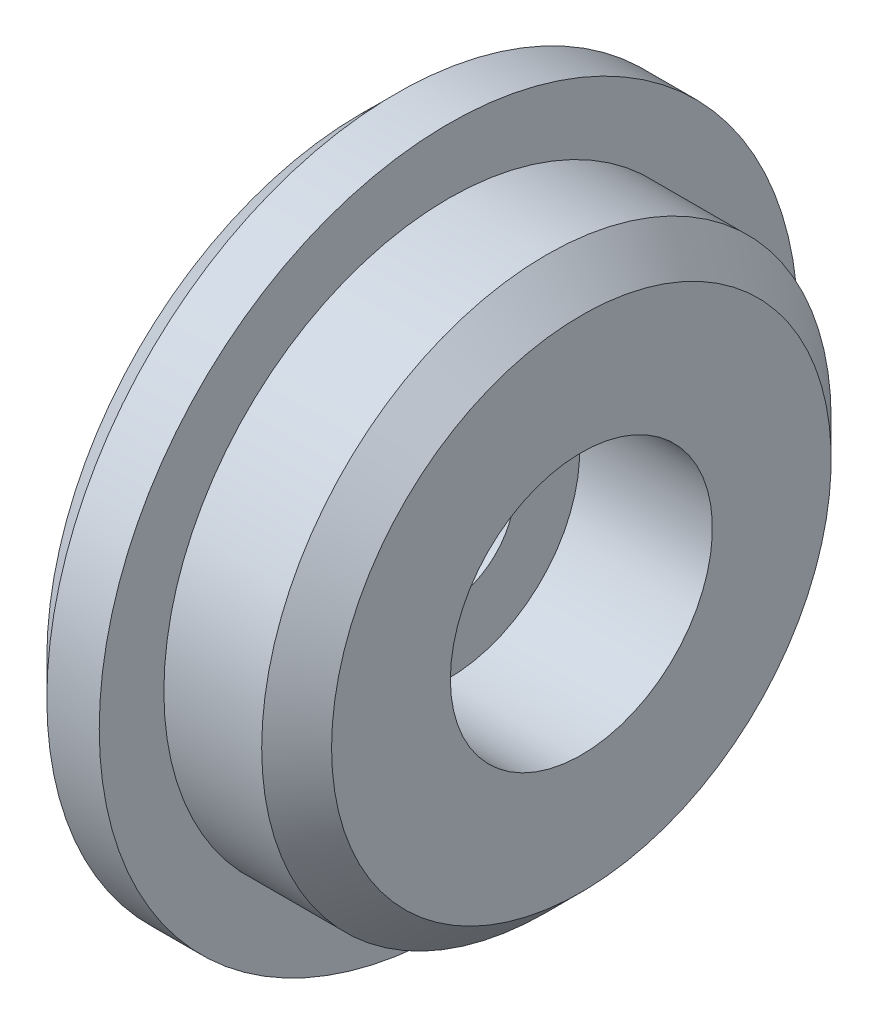
SolidWorks part; units mm, degrees
ref_plane "Front Plane" through (0, 0, 0) normal (0, 0, 1) x (1, 0, 0)
ref_plane "Top Plane" through (0, 0, 0) normal (0, 1, 0) x (1, 0, 0)
ref_plane "Right Plane" through (0, 0, 0) normal (1, 0, 0) x (0, 0, -1)
sketch "Sketch1" plane through (0, 0, 0) normal (0, 0, 1) x (1, 0, 0)
  line L0 (-1.7192, 0) -> (3.3699, 0) construction
  line L1 (0, 0.19) -> (0, 1)
  line L2 (0, 1) -> (0.25, 1)
  line L3 (0.25, 1) -> (0.25, 0.815)
  line L4 (0.25, 0.815) -> (0.63, 0.815)
  line L5 (0.63, 0.815) -> (0.63, 0.375)
  line L6 (0.63, 0.375) -> (0.25, 0.375)
  line L7 (0.25, 0.375) -> (0.25, 0.19)
  line L8 (0.25, 0.19) -> (0, 0.19)
  dimension "D1" = 1
  dimension "D2" = 0.815
  dimension "D3" = 0.19
  dimension "D4" = 0.375
  dimension "D5" = 0.25
  dimension "D6" = 0.38
  dimension "D7" = 0.185
  dimension "D8" = 0.25
  dimension "D9" = 0.38
revolve "Revolve1" add sketch "Sketch1" angle 360 about L0
chamfer "Chamfer1" distance 0.1 angle 45 2 edges at (0, 0, 1) (0.63, 0, 0.815)
